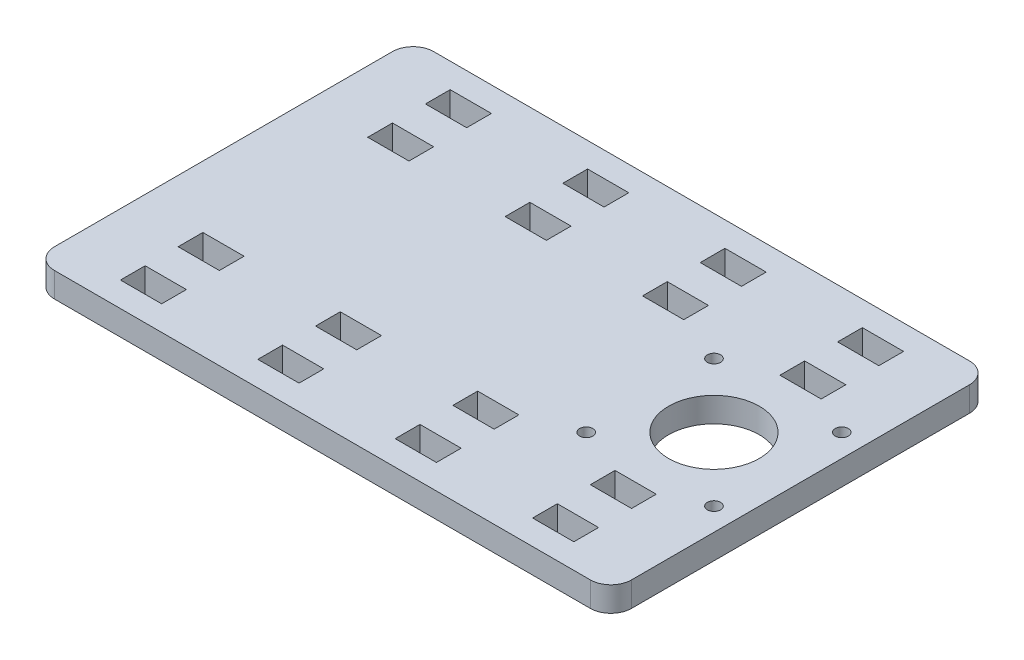
SolidWorks part; units mm, degrees
material "Maple"
ref_plane "Front Plane" through (0, 0, 0) normal (0, 0, 1) x (1, 0, 0)
ref_plane "Top Plane" through (0, 0, 0) normal (0, 1, 0) x (1, 0, 0)
ref_plane "Right Plane" through (0, 0, 0) normal (1, 0, 0) x (0, 0, -1)
sketch "Sketch1" plane through (0, 0, 0) normal (0, 1, 0) x (1, 0, 0)
  line L1 (-70, 46) -> (70, 46)
  line L2 (-70, 46) -> (-70, -46)
  line L3 (-70, -46) -> (70, -46)
  line L4 (70, 46) -> (70, -46)
  line L5 (-70, 46) -> (70, -46) construction
  line L6 (-70, -46) -> (70, 46) construction
  point P0 (0, 0)
  dimension "D1" = 140
  dimension "D2" = 92
extrude "Boss-Extrude1" add sketch "Sketch1" along normal blind 6
ref_plane "Plane1" through (0, 3, 0) normal (0, 1, 0) x (1, 0, 0)
ref_plane "Plane2" through (0, 0, 0) normal (0, 0, 1) x (1, 0, 0)
sketch "Sketch2" plane through (0, 6, 0) normal (0, 1, 0) x (1, 0, 0)
  line L0 (-70, 0) -> (70, 0) construction
  line L1 (-70, 46) -> (-70, -46) construction
  line L2 (70, -46) -> (70, 46) construction
  line L4 (40, 10) -> (70, 10)
  line L5 (40, 10) -> (40, -10)
  line L6 (40, -10) -> (70, -10)
  line L7 (70, 10) -> (70, -10)
  dimension "D1" = 30
  dimension "D2" = 20
extrude "Cut-Extrude1" [suppressed] cut sketch "Sketch2" against normal through all
sketch "Sketch3" plane through (0, 6, 0) normal (0, 1, 0) x (1, 0, 0)
  circle A0 centre (49, 0) radius 11 construction
  circle A1 centre (33.5, -15.5) radius 1.6 construction
  circle A2 centre (33.5, 15.5) radius 1.6 construction
  circle A3 centre (64.5, 15.5) radius 1.6 construction
  circle A4 centre (64.5, -15.5) radius 1.6 construction
  circle A5 centre (49, 0) radius 11
  circle A6 centre (33.5, -15.5) radius 1.6
  circle A7 centre (33.5, 15.5) radius 1.6
  circle A8 centre (64.5, 15.5) radius 1.6
  circle A9 centre (64.5, -15.5) radius 1.6
extrude "Cut-Extrude2" cut sketch "Sketch3" against normal through all
sketch "Sketch4" plane through (0, 6, 0) normal (0, 1, 0) x (1, 0, 0)
  line L0 (-70, 37) -> (70, 37) construction
  line L1 (-70, 46) -> (-70, -46) construction
  line L2 (70, -46) -> (70, 46) construction
  line L3 (-50, 37) -> (-16.6667, 37) construction
  line L5 (70, 46) -> (-70, 46) construction
  point P6 (-50, 37)
  point P7 (-16.6667, 37)
  point P9 (16.6667, 37)
  point P10 (50, 37)
  dimension "D2" = 100
  dimension "D3" = 20
  dimension "D4" = 9
  dimension "D1" = 4
sketch "Sketch6" plane through (49.2322, 3, -81) normal (0, 1, 0) x (1, 0, 0)
  line L1 (-4.2322, -41) -> (5.7678, -41)
  line L2 (-4.2322, -41) -> (-4.2322, -47)
  line L3 (-4.2322, -47) -> (5.7678, -47)
  line L4 (5.7678, -41) -> (5.7678, -47)
  line L5 (-4.2322, -41) -> (5.7678, -47) construction
  line L6 (-4.2322, -47) -> (5.7678, -41) construction
  point P0 (0.7678, -44)
  dimension "D1" = 10
  dimension "D2" = 6
extrude "Cut-Extrude12" cut sketch "Sketch6" against normal through all and the other way through all
other "Smart-Feature2<virtual_pin-6>"
sketch "Sketch61" plane through (15.8989, 3, -81) normal (0, 1, 0) x (1, 0, 0)
  line L1 (-4.2322, -41) -> (5.7678, -41)
  line L2 (-4.2322, -41) -> (-4.2322, -47)
  line L3 (-4.2322, -47) -> (5.7678, -47)
  line L4 (5.7678, -41) -> (5.7678, -47)
  line L5 (-4.2322, -41) -> (5.7678, -47) construction
  line L6 (-4.2322, -47) -> (5.7678, -41) construction
  point P0 (0.7678, -44)
  dimension "D1" = 10
  dimension "D2" = 6
extrude "Cut-Extrude14" cut sketch "Sketch61" against normal through all and the other way through all
other "Smart-Feature1<virtual_pin-7>"
sketch "Sketch62" plane through (-17.4344, 3, -81) normal (0, 1, 0) x (1, 0, 0)
  line L1 (-4.2322, -41) -> (5.7678, -41)
  line L2 (-4.2322, -41) -> (-4.2322, -47)
  line L3 (-4.2322, -47) -> (5.7678, -47)
  line L4 (5.7678, -41) -> (5.7678, -47)
  line L5 (-4.2322, -41) -> (5.7678, -47) construction
  line L6 (-4.2322, -47) -> (5.7678, -41) construction
  point P0 (0.7678, -44)
  dimension "D1" = 10
  dimension "D2" = 6
extrude "Cut-Extrude15" cut sketch "Sketch62" against normal through all and the other way through all
other "Smart-Feature2<virtual_pin-8>"
sketch "Sketch63" plane through (-50.7678, 3, -81) normal (0, 1, 0) x (1, 0, 0)
  line L1 (-4.2322, -41) -> (5.7678, -41)
  line L2 (-4.2322, -41) -> (-4.2322, -47)
  line L3 (-4.2322, -47) -> (5.7678, -47)
  line L4 (5.7678, -41) -> (5.7678, -47)
  line L5 (-4.2322, -41) -> (5.7678, -47) construction
  line L6 (-4.2322, -47) -> (5.7678, -41) construction
  point P0 (0.7678, -44)
  dimension "D1" = 10
  dimension "D2" = 6
extrude "Cut-Extrude16" cut sketch "Sketch63" against normal through all and the other way through all
other "Smart-Feature3<virtual_pin-9>"
sketch "Sketch64" plane through (0, 6, 0) normal (0, 1, 0) x (1, 0, 0)
  line L0 (70, 23) -> (-70, 23) construction
  line L1 (70, -46) -> (70, 46) construction
  line L2 (-70, 46) -> (-70, -46) construction
  line L3 (-62.3, 23) -> (-77.7, 23) construction
  line L4 (-50, 23) -> (-16.6667, 23) construction
  point P8 (-50, 23)
  point P9 (-16.6667, 23)
  point P11 (16.6667, 23)
  point P12 (50, 23)
  dimension "D2" = 20
  dimension "D3" = 100
  dimension "D1" = 4
sketch "Sketch65" plane through (49.2322, 3, -67) normal (0, 1, 0) x (1, 0, 0)
  line L1 (-4.2322, -41) -> (5.7678, -41)
  line L2 (-4.2322, -41) -> (-4.2322, -47)
  line L3 (-4.2322, -47) -> (5.7678, -47)
  line L4 (5.7678, -41) -> (5.7678, -47)
  line L5 (-4.2322, -41) -> (5.7678, -47) construction
  line L6 (-4.2322, -47) -> (5.7678, -41) construction
  point P0 (0.7678, -44)
  dimension "D1" = 10
  dimension "D2" = 6
extrude "Cut-Extrude17" cut sketch "Sketch65" against normal through all and the other way through all
other "Smart-Feature4<virtual_pin-14>"
sketch "Sketch66" plane through (15.8989, 3, -67) normal (0, 1, 0) x (1, 0, 0)
  line L1 (-4.2322, -41) -> (5.7678, -41)
  line L2 (-4.2322, -41) -> (-4.2322, -47)
  line L3 (-4.2322, -47) -> (5.7678, -47)
  line L4 (5.7678, -41) -> (5.7678, -47)
  line L5 (-4.2322, -41) -> (5.7678, -47) construction
  line L6 (-4.2322, -47) -> (5.7678, -41) construction
  point P0 (0.7678, -44)
  dimension "D1" = 10
  dimension "D2" = 6
extrude "Cut-Extrude18" cut sketch "Sketch66" against normal through all and the other way through all
other "Smart-Feature5<virtual_pin-15>"
sketch "Sketch67" plane through (-17.4344, 3, -67) normal (0, 1, 0) x (1, 0, 0)
  line L1 (-4.2322, -41) -> (5.7678, -41)
  line L2 (-4.2322, -41) -> (-4.2322, -47)
  line L3 (-4.2322, -47) -> (5.7678, -47)
  line L4 (5.7678, -41) -> (5.7678, -47)
  line L5 (-4.2322, -41) -> (5.7678, -47) construction
  line L6 (-4.2322, -47) -> (5.7678, -41) construction
  point P0 (0.7678, -44)
  dimension "D1" = 10
  dimension "D2" = 6
extrude "Cut-Extrude19" cut sketch "Sketch67" against normal through all and the other way through all
other "Smart-Feature6<virtual_pin-16>"
sketch "Sketch68" plane through (-50.7678, 3, -67) normal (0, 1, 0) x (1, 0, 0)
  line L1 (-4.2322, -41) -> (5.7678, -41)
  line L2 (-4.2322, -41) -> (-4.2322, -47)
  line L3 (-4.2322, -47) -> (5.7678, -47)
  line L4 (5.7678, -41) -> (5.7678, -47)
  line L5 (-4.2322, -41) -> (5.7678, -47) construction
  line L6 (-4.2322, -47) -> (5.7678, -41) construction
  point P0 (0.7678, -44)
  dimension "D1" = 10
  dimension "D2" = 6
extrude "Cut-Extrude110" cut sketch "Sketch68" against normal through all and the other way through all
other "Smart-Feature7<virtual_pin-17>"
mirror "Mirror1" about plane through (0, 0, 0) normal (0, 0, 1) of "Cut-Extrude17", "Cut-Extrude18", "Cut-Extrude19", "Cut-Extrude110", "Cut-Extrude16", "Cut-Extrude15", "Cut-Extrude14", "Cut-Extrude12"
fillet "Fillet1" radius 5 4 edges at (70, 3, 46) (-70, 3, 46) (70, 3, -46) (-70, 3, -46)
